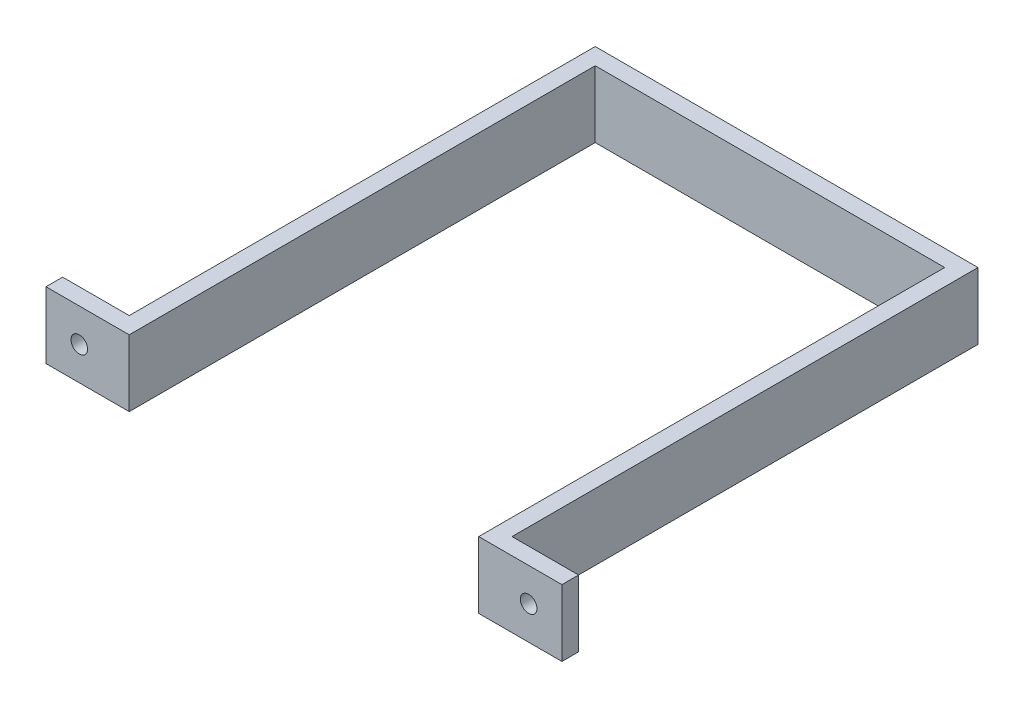
SolidWorks part; units mm, degrees
ref_plane "Front Plane" through (0, 0, 0) normal (0, 0, 1) x (1, 0, 0)
ref_plane "Top Plane" through (0, 0, 0) normal (0, 1, 0) x (1, 0, 0)
ref_plane "Right Plane" through (0, 0, 0) normal (1, 0, 0) x (0, 0, -1)
sketch "Sketch1" plane through (0, 0, 0) normal (0, 1, 0) x (1, 0, 0)
  line L1 (-52.5, 70) -> (52.5, 70)
  line L2 (-52.5, 70) -> (-52.5, -70)
  line L4 (52.5, 70) -> (52.5, -70)
  line L8 (-57.5, -65) -> (-57.5, 75)
  line L9 (-57.5, 75) -> (57.5, 75)
  line L10 (57.5, -65) -> (57.5, 75)
  line L13 (-52.5, -70) -> (-77.5, -70)
  line L14 (-52.5, -70) -> (-52.5, -65)
  line L15 (-57.5, -65) -> (-77.5, -65)
  line L16 (-77.5, -70) -> (-77.5, -65)
  line L17 (52.5, -70) -> (77.5, -70)
  line L18 (52.5, -70) -> (52.5, -65)
  line L19 (57.5, -65) -> (77.5, -65)
  line L20 (77.5, -70) -> (77.5, -65)
  point P0 (0, 0)
  point P6 (0, 0)
  dimension "D1" = 105
  dimension "D2" = 140
  dimension "D3" = 5
  dimension "D4" = 5
  dimension "D5" = 5
  dimension "D6" = 25
  dimension "D7" = 25
  dimension "D8" = 5
extrude "Boss-Extrude1" add sketch "Sketch1" along normal blind 20 contours L17 L20 L19 L10 L9 L8 L15 L16 L13 L2 L1 L4
sketch "Sketch2" plane through (0, 0, 65) normal (0, 0, -1) x (-1, 0, 0)
  circle A0 centre (-67.5, 10) radius 2.5
  circle A1 centre (67.5, 10) radius 2.5
  dimension "D1" = 5
  dimension "D2" = 5
extrude "Cut-Extrude1" cut sketch "Sketch2" against normal blind 20
